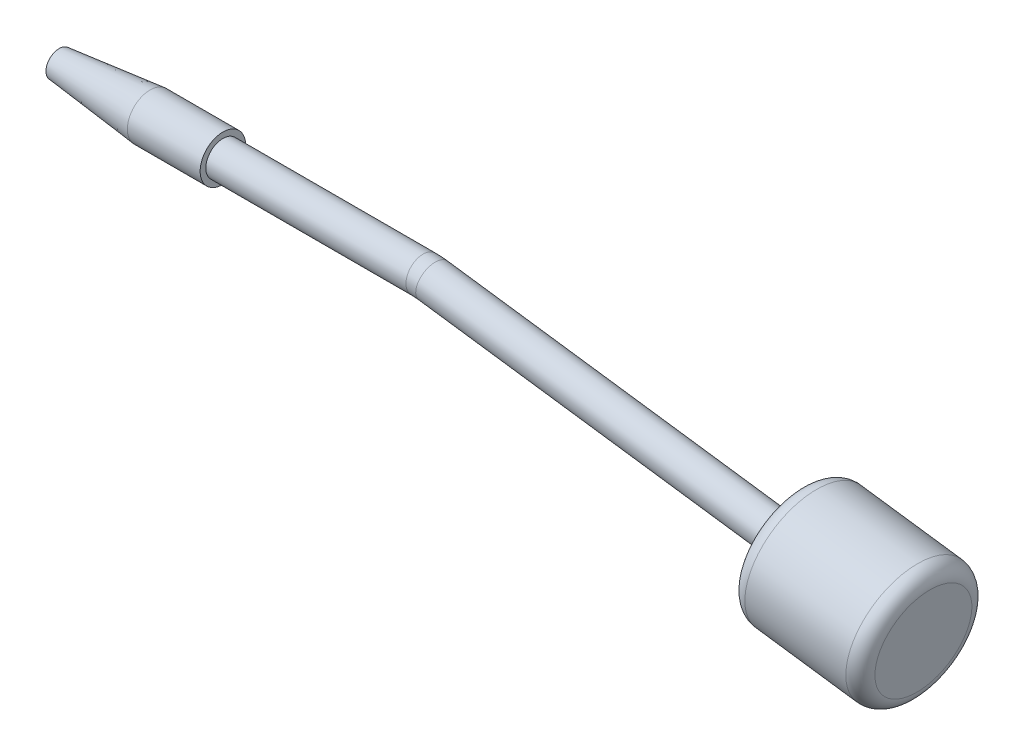
SolidWorks part; units mm, degrees
ref_plane "Front Plane" through (0, 0, 0) normal (0, 0, 1) x (1, 0, 0)
ref_plane "Top Plane" through (0, 0, 0) normal (0, 1, 0) x (1, 0, 0)
ref_plane "Right Plane" through (0, 0, 0) normal (1, 0, 0) x (0, 0, -1)
sketch "Sketch1" plane through (0, 0, 0) normal (0, 0, 1) x (1, 0, 0)
  line L0 (0, 0) -> (-63.5, 0) construction
  line L1 (-63.5, -0.7938) -> (-63.5, -2.286)
  line L2 (-63.5, -2.286) -> (-47.625, -3.9688)
  line L3 (-34.925, -3.9688) -> (-34.925, -2.9845)
  line L4 (-34.925, -2.9845) -> (0, -2.9845)
  line L5 (0, -0.7938) -> (0, -2.9845)
  line L6 (-34.925, -3.9688) -> (-47.625, -3.9688)
  line L7 (-63.5, -0.7938) -> (0, -0.7938)
  dimension "D1" = 28.575
  dimension "D2" = 63.5
  dimension "D3" = 5.969
  dimension "D4" = 4.572
  dimension "D5" = 7.9375
  dimension "D6" = 12.7
  dimension "D7" = 1.5875
revolve "Revolve1" add sketch "Sketch1" angle 360 about L0
sketch "Sketch2" plane through (0, 0, 0) normal (0, 0, 1) x (1, 0, 0)
  line L0 (1.7236, -0.1175) -> (64.6361, -8.7354)
  line L1 (-34.925, -2.9845) -> (0, -2.9845) construction
  line L2 (0, 0) -> (-34.925, 0) construction
  line L3 (-34.925, -2.9845) -> (-34.925, 2.9845) construction
  arc A0 (0, 0) -> (1.7236, -0.1175) centre (0, -12.7) cw
  dimension "D1" = 12.7
  dimension "D2" = 172.2
  dimension "D3" = 63.5
sweep "Sweep1" add path "Sketch2" circular profile diameter 5.969 parameters "D3"=5.969
sketch "Sketch15" plane through (0, 0, 0) normal (0, 0, 1) x (1, 0, 0)
  line L0 (64.6361, -8.7354) -> (87.2846, -11.8379) construction
  line L1 (64.231, -11.6923) -> (65.0411, -5.7786) construction
  line L2 (87.2846, -11.8379) -> (85.8023, -22.6588)
  line L3 (85.8023, -22.6588) -> (63.1538, -19.5564)
  line L4 (63.1538, -19.5564) -> (64.6361, -8.7354)
  line L6 (1.3185, -3.0744) -> (64.231, -11.6923) construction
  line L7 (64.6361, -8.7354) -> (87.2846, -11.8379)
  point P4 (87.2827, -11.8514)
  dimension "D1" = 21.844
  dimension "D2" = 22.86
revolve "Revolve2" add sketch "Sketch15" angle 360 about L0
fillet "Fillet1" radius 2.54 2 edges at (85.8023, -22.6588, 0) (63.1538, -19.5564, 0)
